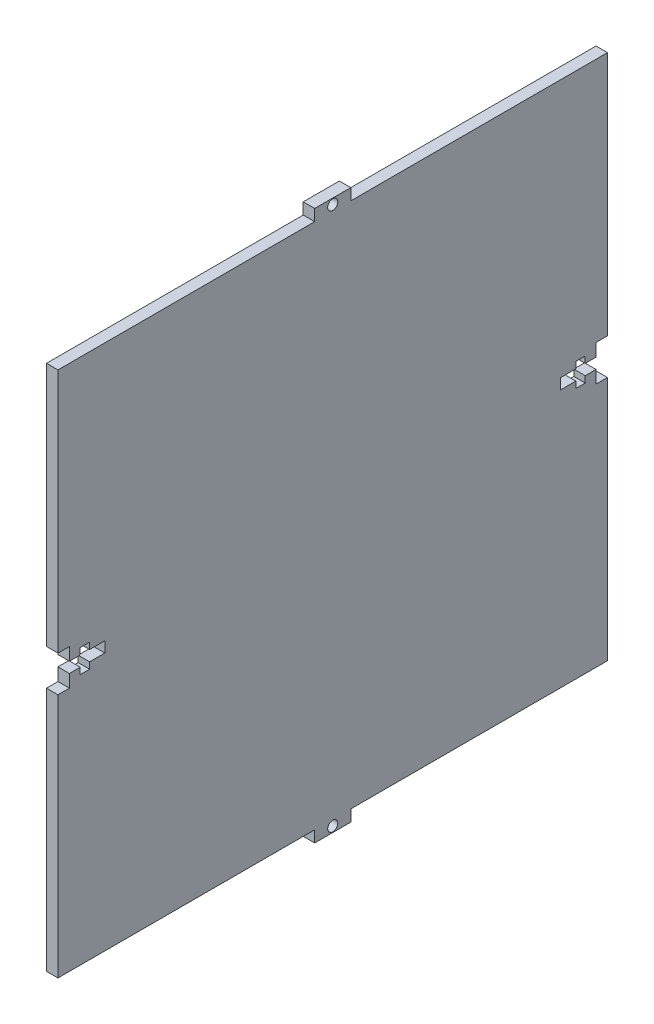
SolidWorks part; units mm, degrees
ref_plane "Front Plane" through (0, 0, 0) normal (0, 0, 1) x (1, 0, 0)
ref_plane "Top Plane" through (0, 0, 0) normal (0, 1, 0) x (1, 0, 0)
ref_plane "Right Plane" through (0, 0, 0) normal (1, 0, 0) x (0, 0, -1)
sketch "Sketch1" plane through (0, 0, 0) normal (1, 0, 0) x (0, 0, -1)
  line L1 (76.2, 73.02) -> (-76.2, 73.02)
  line L2 (76.2, 73.02) -> (76.2, -73.02)
  line L3 (76.2, -73.02) -> (-76.2, -73.02)
  line L4 (-76.2, 73.02) -> (-76.2, -73.02)
  line L5 (76.2, 73.02) -> (-76.2, -73.02) construction
  line L6 (76.2, -73.02) -> (-76.2, 73.02) construction
  point P0 (0, 0)
  dimension "D1" = 146.04
  dimension "D2" = 152.4
extrude "Boss-Extrude1" add sketch "Sketch1" along normal blind 3.18
sketch "Sketch3" plane through (0, 0, 0) normal (-1, 0, 0) x (0, 0, 1)
  line L1 (0, 0) -> (-76.2, 0) construction
  line L2 (-76.2, -73.02) -> (-76.2, 73.02) construction
  line L3 (0, -73.02) -> (0, 73.02) construction
  line L9 (0, 0) -> (76.2, 0) construction
  line L10 (76.2, -73.02) -> (-76.2, -73.02) construction
  line L12 (76.2, 73.02) -> (76.2, -73.02) construction
  line L13 (-76.2, 73.02) -> (76.2, 73.02) construction
  line L14 (5, -73.02) -> (-5, -73.02)
  line L15 (5, -76.2) -> (-5, -76.2)
  line L16 (5, -76.2) -> (5, -73.02)
  line L18 (-5, -76.2) -> (-5, -73.02)
  line L22 (0, -76.2) -> (0, -70.042) construction
  line L23 (5, -74.61) -> (-5, -74.61) construction
  line L27 (5, 73.02) -> (5, 76.2)
  line L28 (5, 76.2) -> (-5, 76.2)
  line L29 (-5, 73.02) -> (-5, 76.2)
  line L30 (5, 74.61) -> (-5, 74.61) construction
  line L31 (0, 73.02) -> (0, 76.2) construction
  line L32 (5, 73.02) -> (-5, 73.02)
  line L33 (0, 57.9987) -> (0, 73.02)
  circle A0 centre (0, -74.61) radius 1.4
  circle A1 centre (0, 74.61) radius 1.4
  point P31 (0, 65.5094)
  line M14 (76.2, 73.02) -> (-76.2, 73.02)
  line M16 (-76.2, -73.02) -> (76.2, -73.02)
  dimension "D5" = 2.8
  dimension "D6" = 2.8
  dimension "D2" = 10
  dimension "D3" = 3.18
  dimension "D4" = 10
  dimension "D1" = 3.18
extrude "Boss-Extrude5" add sketch "Sketch3" against normal blind 3.18 contours L29 L32 L27 L28 A1 M14 | L18 L15 L16 A0 M16
sketch "Sketch4" plane through (0, 0, 0) normal (1, 0, 0) x (0, 0, -1)
  line L2 (0, 0) -> (-76.2, 0) construction
  line L3 (-76.2, 73.02) -> (-76.2, -73.02) construction
  line L4 (-76.2, -5) -> (-76.2, 5)
  line L5 (-76.2, -5) -> (-73.02, -5)
  line L7 (-76.2, 5) -> (-73.02, 5)
  line L8 (-73.02, -5) -> (-73.02, -1.47)
  line L9 (-73.02, 1.47) -> (-73.02, 5)
  line L10 (-73.02, -1.47) -> (-70.02, -1.47)
  line L12 (-73.02, 1.47) -> (-70.02, 1.47)
  line L13 (-63.2, -1.47) -> (-63.2, 1.47)
  line L14 (-67.42, -1.47) -> (-63.2, -1.47)
  line L15 (-70.02, -3.25) -> (-67.42, -3.25)
  line L16 (-70.02, -3.25) -> (-70.02, -1.47)
  line L17 (-70.02, 3.25) -> (-67.42, 3.25)
  line L18 (-67.42, -3.25) -> (-67.42, -1.47)
  line L19 (-67.42, 1.47) -> (-63.2, 1.47)
  line L20 (-70.02, 1.47) -> (-70.02, 3.25)
  line L21 (-67.42, 1.47) -> (-67.42, 3.25)
  dimension "D1" = 3.18
  dimension "D2" = 10
  dimension "D3" = 2.94
  dimension "D4" = 6.5
  dimension "D5" = 2.6
  dimension "D6" = 13
  dimension "D7" = 3
extrude "Cut-Extrude2" cut sketch "Sketch4" along normal through all contours L18 L14 L13 L19 L21 L17 L20 L12 L9 L7 L4 L5 L8 L10 L16 L15
sketch "Sketch5" plane through (0, 0, 0) normal (-1, 0, 0) x (0, 0, 1)
  line L0 (0, 0) -> (-76.2, 0) construction
  line L1 (-76.2, -73.02) -> (-76.2, 73.02) construction
  line L2 (-70.02, -1.47) -> (-73.02, -1.47)
  line L3 (-76.2, -5) -> (-73.02, -5)
  line L4 (-76.2, -5) -> (-76.2, 5)
  line L5 (-76.2, 5) -> (-73.02, 5)
  line L6 (-73.02, -5) -> (-73.02, -1.47)
  line L7 (-63.2, -1.47) -> (-67.42, -1.47)
  line L8 (-63.2, -1.47) -> (-63.2, 1.47)
  line L9 (-63.2, 1.47) -> (-67.42, 1.47)
  line L13 (-67.42, 3.25) -> (-70.02, 3.25)
  line L14 (-67.42, 3.25) -> (-67.42, 1.47)
  line L15 (-67.42, -3.25) -> (-70.02, -3.25)
  line L16 (-70.02, 3.25) -> (-70.02, 1.47)
  line L17 (-70.02, -1.47) -> (-70.02, -3.25)
  line L20 (-67.42, -1.47) -> (-67.42, -3.25)
  line L22 (-70.02, 1.47) -> (-73.02, 1.47)
  line L23 (-73.02, 1.47) -> (-73.02, 5)
  point P9 (-39.8999, 0)
  dimension "D1" = 10
  dimension "D2" = 3.18
  dimension "D3" = 3
  dimension "D4" = 2.6
  dimension "D5" = 2.6
  dimension "D6" = 2.94
  dimension "D7" = 13
  dimension "D8" = 6.5
  dimension "D9" = 6.5
  dimension "D10" = 4.22
extrude "Cut-Extrude3" cut sketch "Sketch5" against normal through all
equation "\"sheet\"= 3.18mm"
equation "\"tabW\"= 15mm"
equation "\"4-40Diam\" = 2.94mm"
equation "\"nutDiam\" = 6.5mm"
equation "\"nutThickness\"= 2.6mm"
